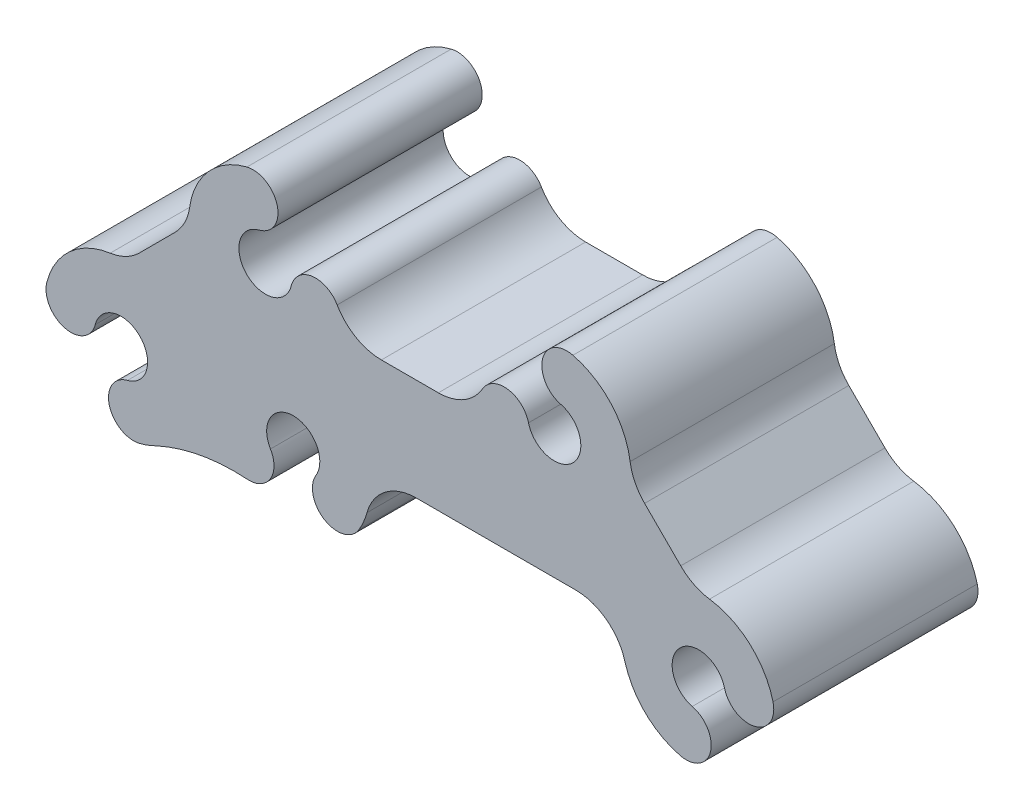
SolidWorks part; units mm, degrees
material "6061-T6 (SS)"
ref_plane "Front Plane" through (0, 0, 0) normal (0, 0, 1) x (1, 0, 0)
ref_plane "Top Plane" through (0, 0, 0) normal (0, 1, 0) x (1, 0, 0)
ref_plane "Right Plane" through (0, 0, 0) normal (1, 0, 0) x (0, 0, -1)
sketch "Sketch1" plane through (0, 0, 0) normal (0, 0, 1) x (1, 0, 0)
  line L0 (-17.9602, 9.525) -> (17.9605, 9.525) construction
  line L1 (3.5417, 6.35) -> (-3.5417, 6.35)
  line L2 (-29.1844, 7.2799) -> (-33.6682, 2.7898)
  line L3 (0.7827, -6.35) -> (20.6295, -6.35)
  line L4 (0, 6.35) -> (0, -44.5381) construction
  line L5 (-59.9264, 0) -> (76.8819, 0) construction
  line L6 (33.6827, 2.7852) -> (29.1915, 7.268)
  line L7 (-35.9196, -8.4391) -> (-14.5039, -8.4391) construction
  arc A1 (27.3908, 10.8674) -> (29.1915, 7.268) centre (33.6774, 11.7623) ccw
  arc A2 (27.3908, 10.8674) -> (20.2758, 18.7647) centre (17.9605, 9.525) ccw
  arc A3 (20.2758, 18.7647) -> (18.7623, 12.7285) centre (19.5195, 15.7465) ccw
  arc A4 (14.7554, 8.7253) -> (18.7623, 12.7285) centre (17.9589, 9.5258) ccw
  arc A5 (14.7554, 8.7253) -> (9.0417, 9.5262) centre (11.7367, 7.971) ccw
  arc A6 (3.5417, 6.35) -> (9.0417, 9.5262) centre (3.5417, 12.7) ccw
  arc A7 (-9.0417, 9.5262) -> (-3.5417, 6.35) centre (-3.5417, 12.7) ccw
  arc A8 (-9.0417, 9.5262) -> (-14.7555, 8.7248) centre (-11.7367, 7.971) ccw
  arc A9 (-18.8235, 12.7132) -> (-14.7555, 8.7248) centre (-17.9602, 9.525) ccw
  arc A10 (-18.8235, 12.7132) -> (-20.2664, 18.7663) centre (-19.513, 15.7474) ccw
  arc A11 (-20.2664, 18.7663) -> (-27.4001, 10.7932) centre (-17.9602, 9.525) ccw
  arc A12 (-29.1844, 7.2799) -> (-27.4001, 10.7932) centre (-33.6745, 11.7701) ccw
  arc A13 (-37.2647, 0.9904) -> (-33.6682, 2.7898) centre (-38.1615, 7.2768) ccw
  arc A14 (-37.2647, 0.9904) -> (-45.1594, -6.1259) centre (-35.9196, -8.4391) ccw
  arc A15 (-45.1594, -6.1259) -> (-39.1227, -7.6372) centre (-42.1411, -6.8815) ccw
  arc A16 (-35.1195, -11.6427) -> (-39.1227, -7.6372) centre (-35.9196, -8.4391) ccw
  arc A17 (-35.1195, -11.6427) -> (-33.6117, -17.6803) centre (-34.3656, -14.6615) ccw
  arc A18 (-33.6117, -17.6803) -> (-31.6466, -16.9519) centre (-35.9196, -8.4391) ccw
  arc A19 (-20.2199, -14.8407) -> (-31.6466, -16.9519) centre (-21.8246, -38.1341) ccw
  arc A20 (-20.2199, -14.8407) -> (-17.3372, -10.1371) centre (-20.0061, -11.7366) ccw
  arc A21 (-11.7446, -10.2547) -> (-17.3372, -10.1371) centre (-14.5039, -8.4391) ccw
  arc A22 (-11.7446, -10.2547) -> (-6.3396, -13.3359) centre (-9.0086, -11.7366) ccw
  arc A23 (-6.3396, -13.3359) -> (-5.3344, -10.996) centre (-14.5101, -8.4401) ccw
  arc A24 (0.7827, -6.35) -> (-5.3344, -10.996) centre (0.7827, -12.7) ccw
  arc A25 (26.7461, -10.9942) -> (20.6295, -6.35) centre (20.6295, -12.7) ccw
  arc A26 (26.7461, -10.9942) -> (33.6131, -17.6767) centre (35.921, -8.4355) ccw
  arc A27 (33.6131, -17.6767) -> (35.121, -11.6391) centre (34.367, -14.6579) ccw
  arc A28 (39.1246, -7.6354) -> (35.121, -11.6391) centre (35.921, -8.4355) ccw
  arc A29 (39.1246, -7.6354) -> (45.1622, -6.1276) centre (42.1434, -6.8815) ccw
  arc A30 (45.1622, -6.1276) -> (37.2696, 0.9935) centre (35.921, -8.4355) ccw
  arc A32 (33.6827, 2.7852) -> (37.2696, 0.9935) centre (38.1686, 7.2796) ccw
  dimension "D1" = 3.1115
  dimension "D2" = 3.302
  dimension "D3" = 7.0835
  dimension "D4" = 12.7
  dimension "D7" = 6.35
  dimension "D8" = 3.1115
  dimension "D9" = 6.35
  dimension "D17" = 6.35
  dimension "D18" = 6.35
  dimension "D15" = 3.1115
  dimension "D10" = 9.5258
  dimension "D22" = 9.5254
  dimension "D23" = 9.525
  dimension "D24" = 33.6774
  dimension "D27" = 11.7701
  dimension "D28" = 33.6745
  dimension "D29" = 15.7474
  dimension "D34" = 20.6295
  dimension "D40" = 9.0086
  dimension "D42" = 9.525
  dimension "D46" = 3.1115
  dimension "D47" = 23.3486
  dimension "D25" = 6.35
  dimension "D6" = 19.8469
  dimension "D11" = 8.4355
  dimension "D12" = 35.921
  dimension "D13" = 39.0325
  dimension "D14" = 11.7367
  dimension "D16" = 15.7465
  dimension "D19" = 7.971
  dimension "D20" = 35.9207
  dimension "D21" = 11.7623
  dimension "D26" = 6.3455
  dimension "D32" = 2.7898
  dimension "D33" = 7.2799
  dimension "D35" = 6.8815
  dimension "D36" = 42.1434
  dimension "D37" = 34.367
  dimension "D38" = 14.6579
  dimension "D39" = 6.8815
  dimension "D41" = 11.7366
  dimension "D44" = 11.7366
  dimension "D45" = 20.0061
  dimension "D48" = 21.8246
  dimension "D49" = 35.9196
  dimension "D50" = 34.3656
extrude "Extrude1" add sketch "Sketch1" along normal mid plane 25.4
